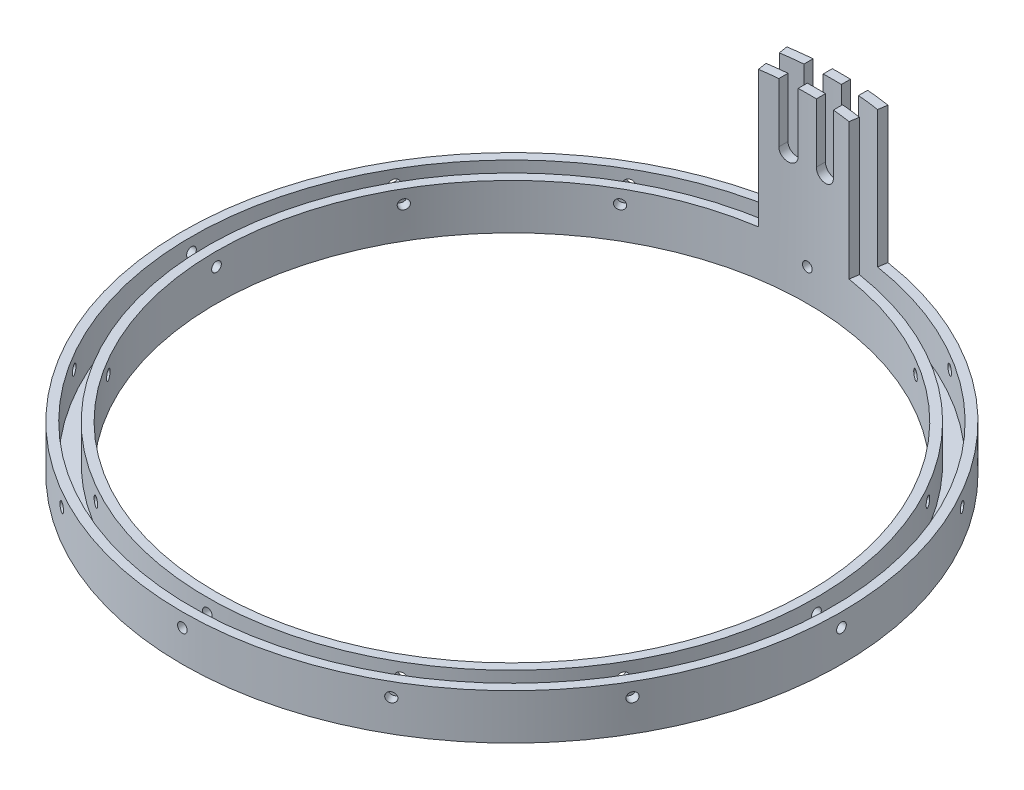
SolidWorks part; units mm, degrees
ref_plane "Front Plane" through (0, 0, 0) normal (0, 0, 1) x (1, 0, 0)
ref_plane "Top Plane" through (0, 0, 0) normal (0, 1, 0) x (1, 0, 0)
ref_plane "Right Plane" through (0, 0, 0) normal (1, 0, 0) x (0, 0, -1)
sketch "Sketch1" plane through (0, 0, 0) normal (0, 1, 0) x (1, 0, 0)
  circle A0 centre (0, 0) radius 92.075
  circle A1 centre (0, 0) radius 82.55
  dimension "D1" = 184.15
  dimension "D2" = 165.1
extrude "Boss-Extrude1" add sketch "Sketch1" along normal blind 12.7
sketch "Sketch3" plane through (0, 0, 0) normal (0, 0, 1) x (1, 0, 0)
  line L0 (92.075, 12.7) -> (-92.075, 12.7) construction
  circle A0 centre (0, 8.89) radius 1.3525
  dimension "D1" = 2.7051
  dimension "D2" = 3.81
extrude "Cut-Extrude2" cut sketch "Sketch3" against normal up to surface (92.0651 mm away)
pattern_circular "CirPattern1" count 12 over 360 about axis through (0, 12.7, 0) along (0, 1, 0) of "Cut-Extrude2"
sketch "Sketch4" plane through (0, 12.7, 0) normal (0, 1, 0) x (1, 0, 0)
  line L0 (-12.7, 81.5672) -> (-14.1654, 90.9788)
  line L1 (12.5999, 81.5827) -> (14.0538, 90.9961)
  line L2 (0, 0) -> (-12.7, 81.5672) construction
  arc A0 (-14.1654, 90.9788) -> (14.0538, 90.9961) centre (0, 0) cw
  circle A1 centre (0, 0) radius 92.075 construction
  arc A2 (-12.7, 81.5672) -> (12.5999, 81.5827) centre (0, 0) cw
  circle A4 centre (0, 0) radius 82.55 construction
  dimension "D2" = 25.4
  dimension "D1" = 12.7
extrude "Boss-Extrude2" add sketch "Sketch4" along normal blind 38.1
sketch "Sketch2" plane through (0, 12.7, 0) normal (0, 1, 0) x (1, 0, 0)
  circle A0 centre (0, 0) radius 85.09
  circle A1 centre (0, 0) radius 89.535
  dimension "D1" = 179.07
  dimension "D2" = 170.18
extrude "Cut-Extrude1" cut sketch "Sketch2" against normal blind 10.16 and the other way up to surface
sketch "Sketch6" plane through (0, 0, 0) normal (0, 0, 1) x (1, 0, 0)
  line L0 (5.08, 59.69) -> (5.08, 34.29) construction
  line L1 (7.62, 59.69) -> (7.62, 34.29)
  line L2 (2.54, 59.69) -> (2.54, 34.29)
  line L3 (-5.08, 59.69) -> (-5.08, 34.29) construction
  line L4 (-2.54, 59.69) -> (-2.54, 34.29)
  line L5 (-7.62, 59.69) -> (-7.62, 34.29)
  circle A2 centre (0, 8.89) radius 1.3525 construction
  arc A3 (7.62, 59.69) -> (2.54, 59.69) centre (5.08, 59.69) ccw
  arc A4 (2.54, 34.29) -> (7.62, 34.29) centre (5.08, 34.29) ccw
  arc A5 (-2.54, 59.69) -> (-7.62, 59.69) centre (-5.08, 59.69) ccw
  arc A6 (-7.62, 34.29) -> (-2.54, 34.29) centre (-5.08, 34.29) ccw
  point P1 (-5.08, 46.99)
  point P6 (5.08, 46.99)
  dimension "D1" = 25.4
  dimension "D2" = 5.08
  dimension "D3" = 10.16
  dimension "D5" = 5.08
  dimension "D6" = 25.4
extrude "Cut-Extrude3" cut sketch "Sketch6" against normal up to surface (91.7591 mm away)
